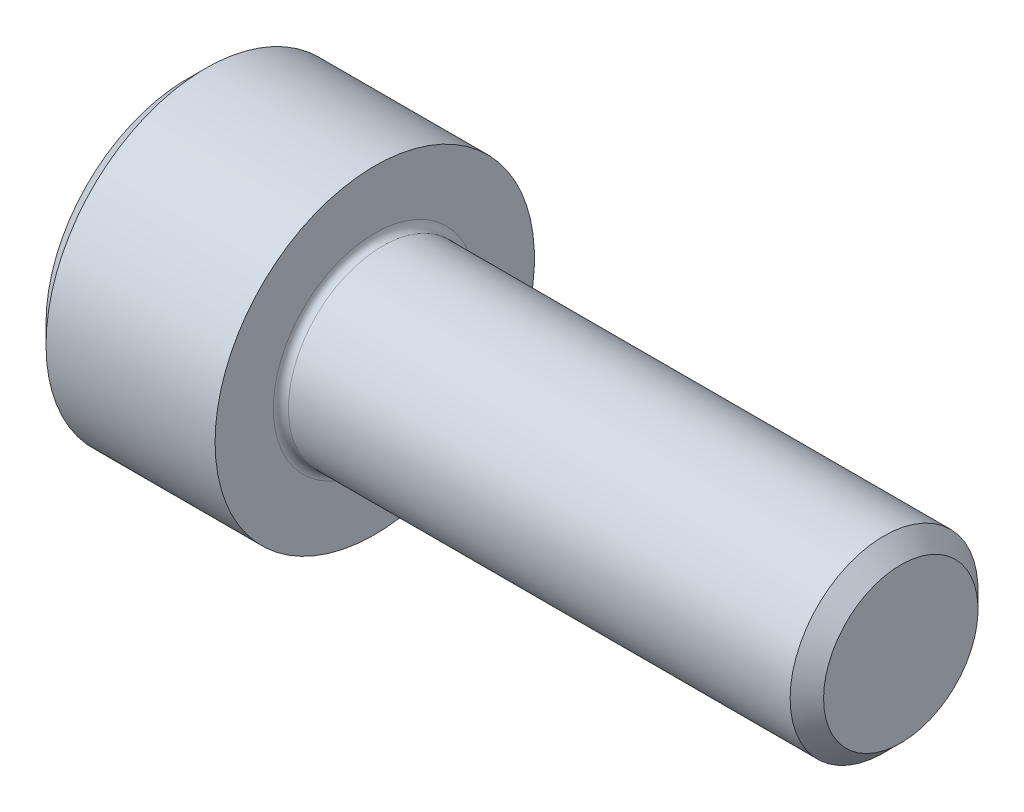
SolidWorks part; units mm, degrees
revolve "Base-Revolve" add sketch "BodySke"
sketch "BodySke" plane through (0, 0, 0) normal (0, 0, 1) x (1, 0, 0)
  line L0 (0, 0) -> (0, 3.75)
  line L1 (0.5, 4.25) -> (5, 4.25)
  line L2 (5, 4.25) -> (5, 2.5)
  line L3 (5, 2.5) -> (18.555, 2.5)
  line L4 (19, 2.055) -> (19, 0)
  line L5 (19, 0) -> (0, 0)
  line L6 (-31.75, 0) -> (127, 0) construction
  line L7 (0, 3.75) -> (0.5, 4.25)
  line L8 (19, 2.055) -> (18.555, 2.5)
  line L9 (0, -3.75) -> (0.5, -4.25) construction
  line L10 (19, -2.055) -> (18.555, -2.5) construction
  line L11 (5.8, 9.525) -> (5.8, 3.175) construction
  line L12 (5, 9.525) -> (5, 3.175) construction
  line L13 (-31, 9.525) -> (-31, 3.175) construction
  dimension "Diameter" = 5
  dimension "Head_ht" = 5
  dimension "Length" = 14
  dimension "Body_ch_ang" = 45
  dimension "Head_dia" = 8.5
  dimension "Head_ch_ang" = 45
  dimension "Minor_dia" = 4.11
  dimension "Advance" = 0.8
  dimension "Thread_nom" = 14
  dimension "Thread_length" = 50
  dimension "Head_ch_ht" = 0.5
cosmetic thread "ThreadCosmetic"
fillet "Fillet1" radius 0.2 1 edges at (5, 0, 2.5)
ref_plane "Plane1" through (0, 0, 0) normal (0, 0, 1) x (1, 0, 0)
ref_plane "Plane2" through (0, 0, 0) normal (0, 1, 0) x (1, 0, 0)
ref_plane "Plane3" through (0, 0, 0) normal (1, 0, 0) x (0, 0, -1)
sketch "Sketch2" plane through (0, 0, 0) normal (0, 0, 1) x (1, 0, 0)
  line L0 (0, 2.042) -> (2.5, 2.042)
  line L1 (2.5, 2.042) -> (3.6789, 0)
  line L2 (-31.75, 0) -> (127, 0) construction
  line L3 (3.6789, 0) -> (0, 0)
  line L4 (0, 0) -> (0, 2.042)
  line L5 (0, 3.75) -> (0, -3.75) construction
  line L6 (0, 0) -> (47.625, 0) construction
  line L7 (5, -4.25) -> (5, 4.25) construction
  dimension "D1" = 2.042
  dimension "D2" = 60
revolve "Hex-PreBroach" cut sketch "Sketch2" angle 360 about L6
sketch "Sketch3" plane through (0, 0, 0) normal (-1, 0, 0) x (0, 0.5, 0.866)
  line L0 (1.1789, 2.042) -> (-1.1789, 2.042)
  line L1 (-1.1789, 2.042) -> (-2.3579, 0)
  line L2 (1.1789, 2.042) -> (2.3579, 0)
  line L3 (1.1789, -2.042) -> (2.3579, 0)
  line L4 (1.1789, -2.042) -> (-1.1789, -2.042)
  line L5 (-1.1789, -2.042) -> (-2.3579, 0)
  dimension "D1" = 2.042
  dimension "D2" = 2.042
  dimension "Hex_size" = 4.084
extrude "Hex" cut sketch "Sketch3" against normal blind 2.5
sketch "Sketch4" plane through (0, 0, 0) normal (-1, 0, 0) x (0, 0, 1)
  line L0 (0, 0) -> (2.3876, 0)
  line L1 (0, 0) -> (6.1484, 3.5498) construction
  line L2 (0, 0) -> (1.1938, 2.0677)
  line L3 (1.9883, 0.576) -> (2.2704, 0.7389)
  line L4 (1.493, 1.4339) -> (1.7751, 1.5968)
  arc A0 (1.9883, 0.576) -> (1.493, 1.4339) centre (0, 0) ccw
  arc A1 (2.3876, 0) -> (2.2704, 0.7389) centre (0, 0) ccw
  arc A2 (1.1938, 2.0677) -> (1.7751, 1.5968) centre (0, 0) cw
  dimension "D1" = 30
  dimension "D2" = 60
  dimension "Spline_p_dim" = 0.9906
  dimension "D3" = 0.4953
extrude "Spline" [suppressed] cut sketch "Sketch4" against normal blind 2.5
pattern_circular "CirPattern1" [suppressed] count 6 every 60
sketch "Sketch5" plane through (0, 0, 0) normal (0, 0, 1) x (1, 0, 0)
  line L0 (-31.75, 0) -> (127, 0) construction
  line L2 (0, 3.75) -> (0, -3.75) construction
  circle A0 centre (2, 0) radius 0.675
  dimension "Drilled_hole_dia" = 1.35
  dimension "Drilled_hole_loc" = 2
extrude "Hole" [suppressed] cut sketch "Sketch5" against normal through all and the other way through all
pattern_circular "Drilled-4" [suppressed] count 2 every 60
pattern_circular "Drilled-6" [suppressed] count 3 every 60
sketch "ThdSchSke" plane through (0, 0, 0) normal (0, 0, 1) x (1, 0, 0)
  line L0 (5.8, -2.055) -> (5.4884, -2.5)
  line L1 (5.8, -2.055) -> (6.1116, -2.5)
  line L2 (6.1116, -2.5) -> (6.1116, -3.125)
  line L3 (-3.175, 0) -> (5.1513, 0) construction
  line L5 (6.1116, -3.125) -> (5.4884, -3.125)
  line L6 (5.4884, -3.125) -> (5.4884, -2.5)
  line L7 (0, 3.75) -> (0, -3.75) construction
  dimension "Thread_minor" = 4.11
  dimension "Diameter" = 5
  dimension "Start" = 5.8
revolve "ThreadSchematic" [suppressed] cut sketch "ThdSchSke" angle 360 about L3
pattern_linear "ThdSchPat" [suppressed]
equation "\"D2@Sketch3\" = \"Hex_size@Sketch3\" / 2"
equation "\"D1@Sketch3\" = \"Hex_size@Sketch3\" / 2"
equation "\"D1@Sketch2\" = \"Hex_size@Sketch3\" / 2"
equation "\"D3@Sketch4\" = \"Spline_p_dim@Sketch4\" / 2"
equation "\"Thread_minor@ThreadCosmetic\"  =  \"Minor_dia@BodySke\""
equation "\"D2@CirPattern1\" = 360 / \"Num_teeth@CirPattern1\""
equation "\"Wall_thickness@Sketch2\" = \"Head_ht@BodySke\" - \"Key_eng@Hex\""
equation "\"Thread_length@ThreadCosmetic\" = ((sgn( (\"Length@BodySke\" - \"Advance@BodySke\" ) - \"Thread_nom@BodySke\" )-1)*( (\"Length@BodySke\" - \"Advance@BodySke\" ) - \"Thread_nom@BodySke\" ))/-2+ \"Thread_nom@BodySke\""
equation "\"Thread_minor@ThdSchSke\" = \"Minor_dia@BodySke\""
equation "\"Diameter@ThdSchSke\" = \"Diameter@BodySke\""
equation "\"Overcut@ThdSchSke\" = \"Diameter@BodySke\" * 1.25"
equation "\"Start@ThdSchSke\" = \"Head_ht@BodySke\" + \"Length@BodySke\" - \"Thread_length@ThreadCosmetic\"  '---Non-countersunk---"
equation "\"Num_threads@ThdSchPat\" = int( \"Thread_length@ThreadCosmetic\" / \"Advance@BodySke\" + 0.999 )  + 1"
equation "\"Advance@ThdSchPat\" = \"Thread_length@ThreadCosmetic\" /  (\"Num_threads@ThdSchPat\" - 1) 'relax it"
equation "\"Num_threads@ThdSchPat\" = \"Num_threads@ThdSchPat\" - sgn( \"Num_threads@ThdSchPat\" - 1) '---chamfered tips only---"
